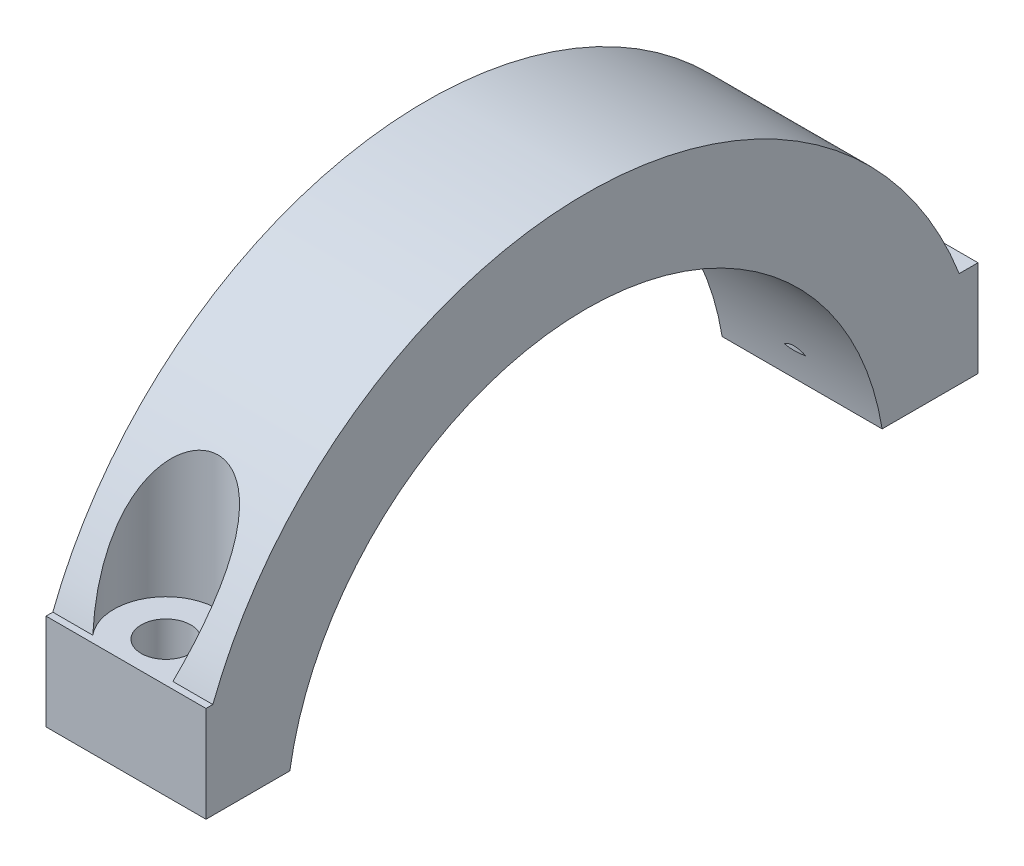
SolidWorks part; units mm, degrees
ref_plane "Front Plane" through (0, 0, 0) normal (0, 0, 1) x (1, 0, 0)
ref_plane "Top Plane" through (0, 0, 0) normal (0, 1, 0) x (1, 0, 0)
ref_plane "Right Plane" through (0, 0, 0) normal (1, 0, 0) x (0, 0, -1)
sketch "Sketch1" plane through (0, 0, 0) normal (1, 0, 0) x (0, 0, -1)
  line L0 (-25, 0) -> (-18.75, 0)
  line L1 (18.75, 0) -> (25, 0)
  arc A0 (18.75, 0) -> (-18.75, 0) centre (0, 0) ccw
  arc A1 (25, 0) -> (-25, 0) centre (0, 0) ccw
  dimension "D1" = 37.5
  dimension "D2" = 50
extrude "Boss-Extrude1" add sketch "Sketch1" along normal blind 10
sketch "Sketch2" plane through (10, 0, 0) normal (1, 0, 0) x (0, 0, -1)
  line L0 (-25, 0) -> (-25, 5)
  line L1 (-25, 5) -> (-18.75, 5)
  line L2 (-18.75, 5) -> (-18.75, 0)
  line L4 (18.75, 0) -> (25, 0)
  line L5 (18.75, 0) -> (18.75, 5)
  line L6 (18.75, 5) -> (25, 5)
  line L7 (25, 0) -> (25, 5)
  arc A0 (25, 0) -> (-25, 0) centre (0, 0) ccw construction
  arc M5 (25, 0) -> (-25, 0) centre (0, 0) ccw
  dimension "D1" = 5
  dimension "D2" = 5
extrude "Boss-Extrude2" add sketch "Sketch2" against normal up to surface (10 mm away) contours L1 L0 M5 | L7 L6 M5 up to face at (0, 10.9375, 0)
sketch "Sketch4" plane through (0, 0, 0) normal (0, 1, 0) x (1, 0, 0)
  line L0 (5, -21.25) -> (5, 21.25) construction
  line L3 (10, -18.75) -> (0, -18.75) construction
  line L4 (10, 18.75) -> (0, 18.75) construction
  line L5 (10, 18.75) -> (10, 25) construction
  circle A0 centre (5, -21.25) radius 1.5
  circle A1 centre (5, 21.25) radius 1.5
  dimension "D1" = 3
  dimension "D2" = 3
  dimension "D4" = 2.5
  dimension "D3" = 5
  dimension "D5" = 2.5
extrude "Cut-Extrude1" cut sketch "Sketch4" against normal through all and the other way through all
sketch "Sketch5" plane through (0, 5, 0) normal (0, 1, 0) x (1, 0, 0)
  circle A0 centre (5, -21.25) radius 3.25
  circle A1 centre (5, 21.25) radius 3.25
  dimension "D1" = 6.5
  dimension "D2" = 6.5
extrude "Cut-Extrude4" cut sketch "Sketch5" along normal through all
sketch "Sketch7" plane through (10, 0, 0) normal (1, 0, 0) x (0, 0, -1)
  circle A0 centre (0, 0) radius 25
  circle A1 centre (0, 0) radius 29.0909
extrude "Cut-Extrude7" cut sketch "Sketch7" against normal through all contours A1 | A0
sketch "Sketch6" plane through (0, 0, 0) normal (0, -1, 0) x (1, 0, 0)
  line L11 (-10.8262, 25.8105) -> (33.7138, 25.8105)
  line L12 (-10.8262, 25.8105) -> (-10.8262, -27.0143)
  line L13 (-10.8262, -27.0143) -> (33.7138, -27.0143)
  line L14 (33.7138, 25.8105) -> (33.7138, -27.0143)
extrude "Cut-Extrude6" cut sketch "Sketch6" against normal blind 3
sketch "Sketch8" plane through (0, 5, 0) normal (0, 1, 0) x (1, 0, 0)
  circle A0 centre (5, 21.25) radius 1.5
  circle A1 centre (5, 21.25) radius 3.25
  arc A2 (4.818, 24.4949) -> (4.3242, 18.071) centre (5, 21.25) ccw construction
  circle A3 centre (5, 21.25) radius 1.5 construction
  circle A4 centre (5, -21.25) radius 1.5
  circle A5 centre (5, -21.25) radius 3.25
  circle A6 centre (5, -21.25) radius 1.5 construction
  arc A7 (4.3242, -18.071) -> (4.818, -24.4949) centre (5, -21.25) ccw construction
extrude "Boss-Extrude3" add sketch "Sketch8" along normal blind 4
sketch "Sketch11" plane through (0, 3, 0) normal (0, -1, 0) x (1, 0, 0)
  line L0 (10, 24.8193) -> (10, 18.5084) construction
  line L1 (0, 18.5084) -> (10, 18.5084)
  line L2 (0, 18.5084) -> (0, 24.5)
  line L3 (0, 24.5) -> (10, 24.5)
  line L4 (10, 18.5084) -> (10, 24.5)
  line L5 (0, -18.5084) -> (10, -18.5084)
  line L6 (0, -18.5084) -> (0, -24.5)
  line L7 (0, -24.5) -> (10, -24.5)
  line L8 (10, -18.5084) -> (10, -24.5)
  arc A0 (4.3242, 18.071) -> (5.6758, 18.071) centre (5, 21.25) ccw construction
  arc A1 (5.6758, -18.071) -> (4.3242, -18.071) centre (5, -21.25) ccw construction
extrude "Boss-Extrude4" add sketch "Sketch11" against normal up to surface (6 mm away) up to face at (5, 9, -21.25)
sketch "Sketch12" plane through (0, 9, 0) normal (0, 1, 0) x (1, 0, 0)
  circle A0 centre (5, 21.25) radius 1.55
  circle A1 centre (5, -21.25) radius 1.55
  arc A2 (7.5024, -23.3238) -> (2.4976, -23.3238) centre (5, -21.25) ccw construction
  arc A3 (2.4976, 23.3238) -> (7.5024, 23.3238) centre (5, 21.25) ccw construction
  dimension "D1" = 3.1
  dimension "D2" = 3.1
extrude "Cut-Extrude8" cut sketch "Sketch12" against normal through all both and the other way through all
sketch "Sketch14" plane through (10, 0, 0) normal (1, 0, 0) x (0, 0, -1)
  line L1 (-24.5, 9) -> (-33.999, 9)
  line L2 (-24.5, 9) -> (-24.5, -2.9565)
  line L3 (-24.5, -2.9565) -> (-33.999, -2.9565)
  line L4 (-33.999, 9) -> (-33.999, -2.9565)
  line L5 (24.5, 9) -> (30.7015, 9)
  line L6 (24.5, 9) -> (24.5, 0.9336)
  line L7 (24.5, 0.9336) -> (30.7015, 0.9336)
  line L8 (30.7015, 9) -> (30.7015, 0.9336)
extrude "Cut-Extrude9" cut sketch "Sketch14" against normal through all both
sketch "Sketch15" plane through (10, 0, 0) normal (1, 0, 0) x (0, 0, -1)
  line L0 (-24.5, 9) -> (-24.5, 3) construction
  line L1 (-28.6268, 11.9381) -> (-23.75, 11.9381)
  line L2 (-28.6268, 11.9381) -> (-28.6268, -0.6484)
  line L3 (-28.6268, -0.6484) -> (-23.75, -0.6484)
  line L4 (-23.75, 11.9381) -> (-23.75, -0.6484)
  dimension "D1" = 0.75
extrude "Cut-Extrude10" cut sketch "Sketch15" against normal through all both
